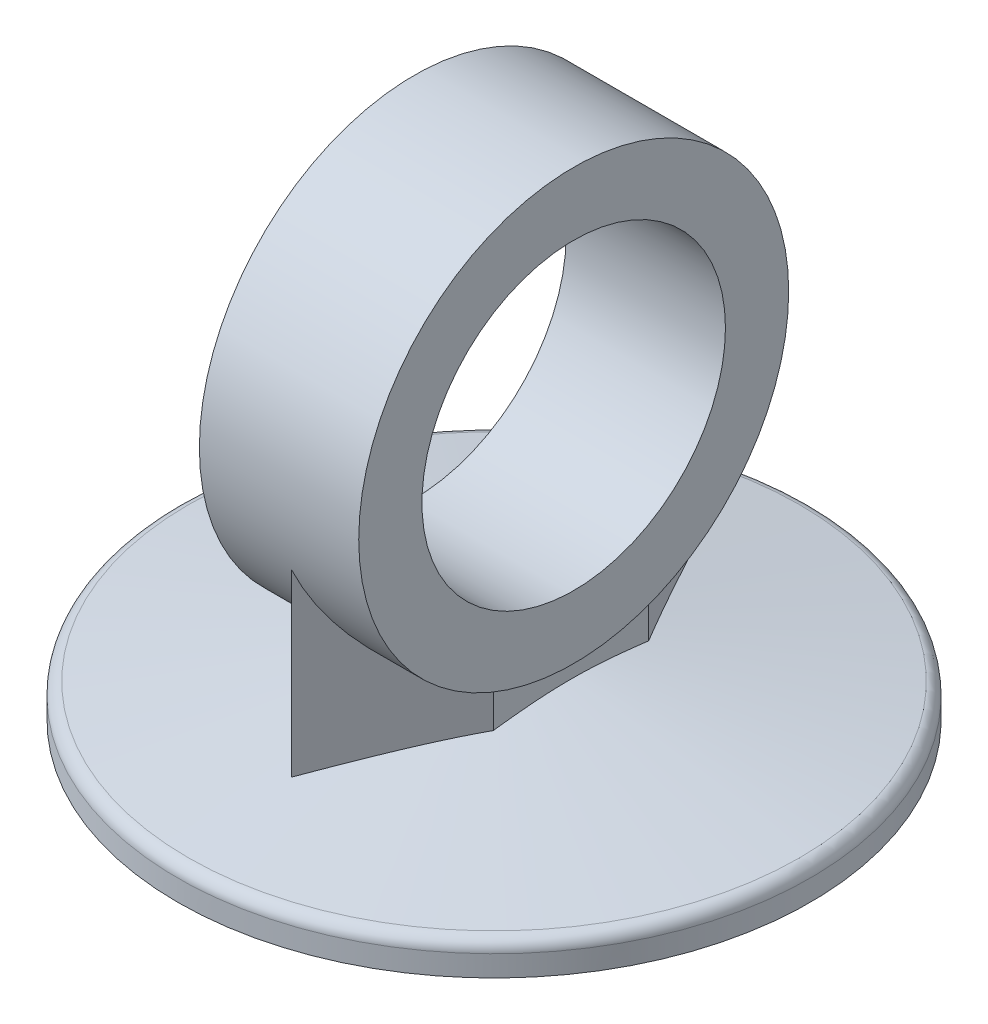
SolidWorks part; units mm, degrees
ref_plane "Front Plane" through (0, 0, 0) normal (0, 0, 1) x (1, 0, 0)
ref_plane "Top Plane" through (0, 0, 0) normal (0, 1, 0) x (1, 0, 0)
ref_plane "Right Plane" through (0, 0, 0) normal (1, 0, 0) x (0, 0, -1)
sketch "Sketch1" plane through (0, 0, 0) normal (0, 1, 0) x (1, 0, 0)
  circle A0 centre (0, 0) radius 25
extrude "Boss-Extrude1" add sketch "Sketch1" along normal blind 2.5
sketch "Sketch2" plane through (0, 0, 0) normal (0, 1, 0) x (1, 0, 0)
  circle A0 centre (0, 0) radius 25
extrude "Boss-Extrude3" add sketch "Sketch2" along normal blind 5 draft 80 from offset 2.5
fillet "Fillet1" radius 1 1 edges at (0, 2.5, 25)
ref_plane "Plane1" through (0, 4, 0) normal (0, 1, 0) x (-1, 0, 0)
sketch "Sketch3" plane through (0, 4, 0) normal (0, 1, 0) x (-1, 0, 0)
  circle A0 centre (0, 0) radius 16.4698
sketch "Sketch4" plane through (0, 4, 0) normal (0, 1, 0) x (-1, 0, 0)
  line L0 (-6.0858, -6.1432) -> (0, -16.0133)
  line L3 (0, -16.0133) -> (6.0858, -6.1432)
  line L4 (-6.0858, 6.1432) -> (0, 16.0133)
  line L5 (0, 16.0133) -> (6.0858, 6.1432)
  line L7 (6.0858, 6.1432) -> (6.0858, -6.1432)
  line L8 (6.0858, 0) -> (6.0858, 6.1432)
  line L9 (-6.0858, 6.1432) -> (-6.0858, -6.1432)
  point P20 (-6.0858, 0)
extrude "Boss-Extrude9" add sketch "Sketch4" along normal blind 15 contours L4 L9 L0 L3 L7 L5
sketch "Sketch5" plane through (0, 0, 0) normal (1, 0, 0) x (0, 0, -1)
  circle A0 centre (0, 24) radius 17
extrude "Boss-Extrude11" add sketch "Sketch5" along normal blind 6.3 and the other way blind 6.3
sketch "Sketch6" plane through (0, 0, 0) normal (1, 0, 0) x (0, 0, -1)
  circle A0 centre (0, 24) radius 12
extrude "Cut-Extrude3" cut sketch "Sketch6" against normal blind 6.3 and the other way blind 6.3
